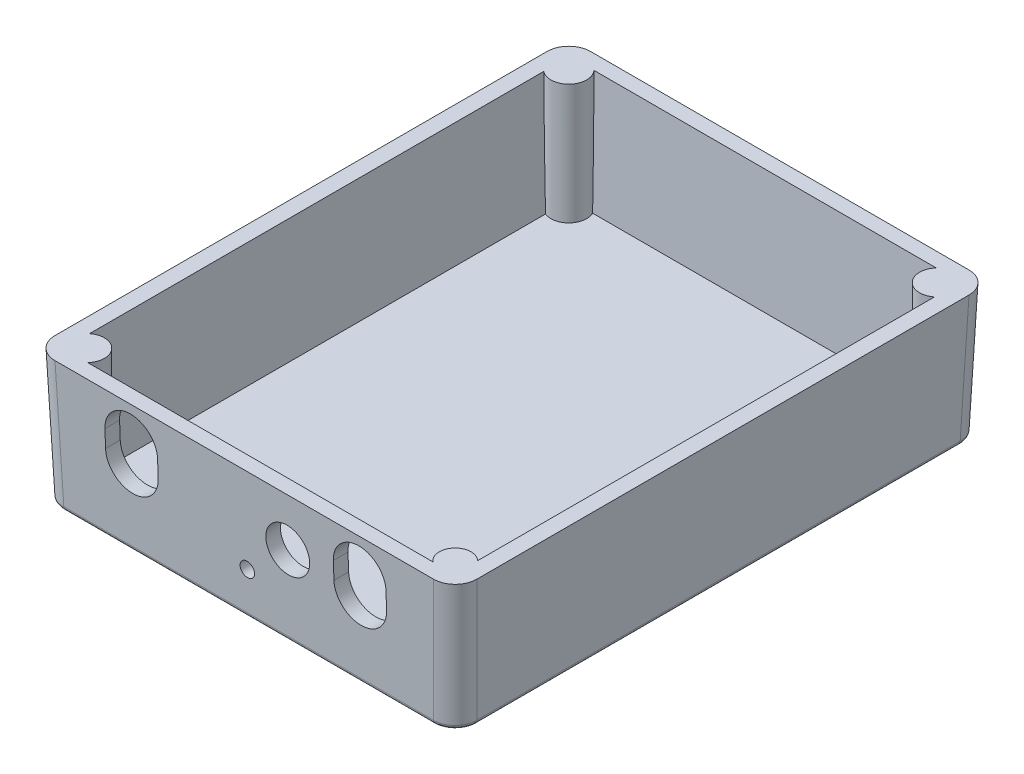
SolidWorks part; units mm, degrees
ref_plane "Front Plane" through (0, 0, 0) normal (0, 0, 1) x (1, 0, 0)
ref_plane "Top Plane" through (0, 0, 0) normal (0, 1, 0) x (1, 0, 0)
ref_plane "Right Plane" through (0, 0, 0) normal (1, 0, 0) x (0, 0, -1)
sketch "Sketch1" plane through (0, 0, 0) normal (0, 1, 0) x (1, 0, 0)
  line L1 (0, 0) -> (94.1, 0)
  line L2 (0, 0) -> (0, 120)
  line L3 (0, 120) -> (94.1, 120)
  line L4 (94.1, 0) -> (94.1, 120)
  dimension "D1" = 94.1
  dimension "D2" = 120
extrude "Boss-Extrude1" add sketch "Sketch1" along normal blind 29.82 draft 2 draft outward yes
fillet "Fillet1" radius 4.95 4 edges at (94.6207, 14.91, 0.5207) (-0.5207, 14.91, 0.5207) (94.6207, 14.91, -120.5207) (-0.5207, 14.91, -120.5207)
ref_plane "Plane1" through (0, 29.82, 0) normal (0, 1, 0) x (1, 0, 0)
sketch "Sketch3" plane through (0, 29.82, 0) normal (0, 1, 0) x (1, 0, 0)
  line L4 (2.52, 2.3) -> (91.58, 2.3)
  line L5 (2.52, 2.3) -> (2.52, 117.7)
  line L6 (2.52, 117.7) -> (91.58, 117.7)
  line L7 (91.58, 2.3) -> (91.58, 117.7)
  line L8 (2.52, 2.3) -> (91.58, 117.7) construction
  line L9 (2.52, 117.7) -> (91.58, 2.3) construction
  point P6 (46.58, 60.47)
  dimension "D1" = 89.06
  dimension "D2" = 115.4
extrude "Cut-Extrude1" cut sketch "Sketch3" against normal blind 27.4 draft 2
sketch "Sketch4" plane through (0, 0, 0) normal (0, 1, 0) x (1, 0, 0)
  circle A0 centre (5.0282, 114.9718) radius 4.065
  circle A1 centre (89.0718, 114.9718) radius 4.065
  circle A2 centre (5.0282, 5.0282) radius 4.065
  circle A3 centre (89.0718, 5.0282) radius 3.6125
extrude "Boss-Extrude2" add sketch "Sketch4" along normal blind 29.82
sketch "Sketch6" plane through (0, 0, 0) normal (0, 0, 1) x (1, 0, 0)
  line L0 (15.015, 21.82) -> (15.015, 17.82)
  line L1 (27.015, 21.82) -> (27.015, 17.82)
  line L3 (67.085, 21.82) -> (67.085, 17.82)
  line L4 (79.085, 21.82) -> (79.085, 17.82)
  circle A0 centre (47.05, 9.82) radius 1.65
  circle A1 centre (21.015, 17.82) radius 6
  circle A2 centre (73.085, 17.82) radius 6
  circle A3 centre (56.575, 18.57) radius 5
  circle A4 centre (21.015, 21.82) radius 6
  circle A5 centre (73.085, 21.82) radius 6
extrude "Cut-Extrude2" cut sketch "Sketch6" against normal blind 8 and the other way through all from offset 3
ref_plane "Plane2" through (0, 0, 0) normal (0, -1, 0) x (-1, 0, 0)
sketch "Sketch8" plane through (0, 0, 0) normal (0, -1, 0) x (-1, 0, 0)
  line L0 (-47.05, 121.0413) -> (-47.05, -1.0413) construction
  line L1 (-90.1944, 121.0413) -> (-3.9056, 121.0413) construction
  line L2 (-3.9056, -1.0413) -> (-90.1944, -1.0413) construction
  line L3 (1.0413, 60) -> (-95.1413, 60) construction
  line L6 (1.0413, 116.0944) -> (1.0413, 3.9056) construction
  line L7 (-95.1413, 3.9056) -> (-95.1413, 116.0944) construction
  circle A0 centre (-71.815, 90.353) radius 2.625
  circle A1 centre (-71.815, 103.053) radius 6.5
extrude "Cut-Extrude3" cut sketch "Sketch8" against normal blind 5
fillet "Fillet2" radius 1 8 edges at (1.4486, 0, -1.4486) (0, 0, -60) (1.4486, 0, -118.5514) (47.05, 0, -120) (92.6514, 0, -118.5514) (94.1, 0, -60) (92.6514, 0, -1.4486) (47.05, 0, 0)
sketch "Sketch9" plane through (0, 0, 0) normal (0, 0, 1) x (1, 0, 0)
  line L0 (21.015, 11.82) -> (21.015, 15.82)
  arc A0 (15.015, 17.82) -> (27.015, 17.82) centre (21.015, 17.82) ccw construction
